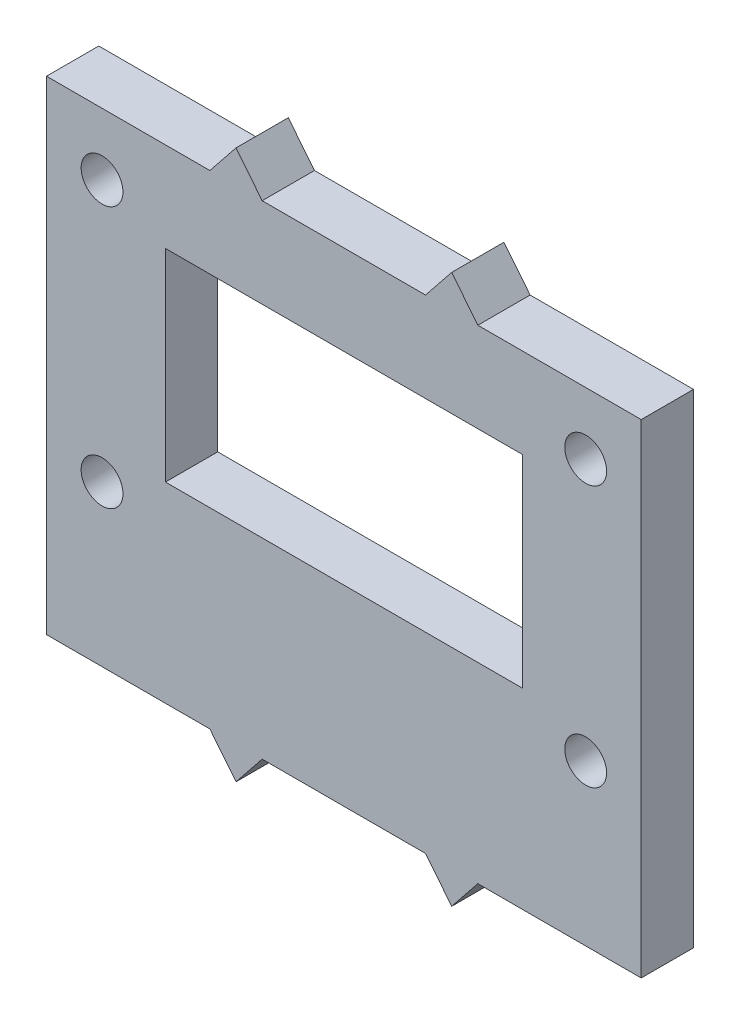
SolidWorks part; units mm, degrees
ref_plane "Front Plane" through (0, 0, 0) normal (0, 0, 1) x (1, 0, 0)
ref_plane "Top Plane" through (0, 0, 0) normal (0, 1, 0) x (1, 0, 0)
ref_plane "Right Plane" through (0, 0, 0) normal (1, 0, 0) x (0, 0, -1)
sketch "Sketch1" plane through (0, 0, 0) normal (0, 0, 1) x (1, 0, 0)
  line L0 (22.75, 37) -> (22.75, 14.7203) construction
  line L1 (0, 0) -> (45.5, 0)
  line L2 (0, 0) -> (0, 37)
  line L3 (0, 37) -> (45.5, 37)
  line L4 (45.5, 0) -> (45.5, 37)
  line L5 (12.5, 37) -> (14.5, 39.5)
  line L6 (14.5, 39.5) -> (16.5, 37)
  line L7 (31, 39.5) -> (29, 37)
  line L8 (33, 37) -> (31, 39.5)
  line L9 (0, 18.5) -> (57.9593, 18.5) construction
  line L10 (33, 0) -> (31, -2.5)
  line L11 (31, -2.5) -> (29, 0)
  line L12 (14.5, -2.5) -> (16.5, 0)
  line L13 (12.5, 0) -> (14.5, -2.5)
  point P9 (22.75, 37)
  point P16 (0, 18.5)
  point P17 (32, 38.25)
  point P18 (32, -1.25)
  dimension "D1" = 37
  dimension "D2" = 45.5
  dimension "D3" = 16.5
  dimension "D4" = 2.5
  dimension "D5" = 4
extrude "Basis" add sketch "Sketch1" along normal blind 4 contours L1 L4 L3 L2 | L6 L5 L3 | L3 L8 L7 | L1 L13 L12 | L11 L10 L1
sketch "Sketch2" [suppressed] plane through (0, 0, 4) normal (0, 0, 1) x (1, 0, 0)
  line L0 (16.5, 37) -> (29, 37) construction
  circle A0 centre (22.75, 23) radius 6.8
  point P5 (22.75, 37)
  dimension "D1" = 13.6
  dimension "D2" = 14
extrude "Camera gat " [suppressed] cut sketch "Sketch2" against normal up to surface (4 mm away)
sketch "Sketch5" [suppressed] plane through (0, 0, 4) normal (0, 0, 1) x (1, 0, 0)
  line L0 (8.6574, 7.1957) -> (36.8426, 7.1957) construction
  line L1 (16.5, 37) -> (29, 37) construction
  text T0 "camera" font "Bebas Kai" height 3.5
  point P2 (22.75, 7.1957)
  point P5 (22.75, 37)
extrude "Cut-Extrude4" [suppressed] cut sketch "Sketch5" against normal blind 0.2
sketch "Sketch3" [suppressed] plane through (0, 0, 4) normal (0, 0, 1) x (1, 0, 0)
  line L0 (22.75, 37) -> (22.75, 0) construction
  line L1 (16.5, 37) -> (29, 37) construction
  line L2 (16.5, 0) -> (29, 0) construction
  line L3 (0, 37) -> (12.5, 37) construction
  circle A0 centre (9.8, 25.6) radius 7.95
  circle A1 centre (35.7, 25.6) radius 7.95
  dimension "D3" = 15.9
  dimension "D1" = 11.4
  dimension "D2" = 25.9
extrude "HR04 gat " [suppressed] cut sketch "Sketch3" against normal up to surface (4 mm away)
sketch "Sketch4" [suppressed] plane through (0, 0, 4) normal (0, 0, 1) x (1, 0, 0)
  line L0 (7.7992, 12.9938) -> (37.7008, 12.9938) construction
  line L1 (16.5, 37) -> (29, 37) construction
  text T0 "AFSTAND SENSOR" font "Bebas Kai" height 3.5
  point P5 (22.75, 12.9938)
  point P8 (22.75, 37)
extrude "Afstand sensor" [suppressed] cut sketch "Sketch4" against normal blind 0.2
sketch "Sketch10" plane through (0, 0, 4) normal (0, 0, 1) x (1, 0, 0)
  line L1 (17.42, 29.57) -> (28.08, 29.57)
  line L2 (17.42, 29.57) -> (17.42, 34.43)
  line L3 (17.42, 34.43) -> (28.08, 34.43)
  line L4 (28.08, 29.57) -> (28.08, 34.43)
  line L5 (17.42, 29.57) -> (28.08, 34.43) construction
  line L6 (17.42, 34.43) -> (28.08, 29.57) construction
  line L9 (16.5, 37) -> (29, 37) construction
  point P4 (22.75, 32)
  point P5 (22.75, 37)
  point P6 (22.75, 34.43)
  dimension "D1" = 4.86
  dimension "D2" = 10.66
  dimension "D3" = 32
extrude "Press_fit" [suppressed] cut sketch "Sketch10" against normal blind 10
sketch "Sketch6" plane through (0, 0, 4) normal (0, 0, 1) x (1, 0, 0)
  line L4 (16.5, 37) -> (29, 37) construction
  point P0 (22.75, 30.14)
  point P3 (22.75, 37)
  line B0 (9.1, 30.14) -> (36.4, 30.14)
  line B1 (9.1, 30.14) -> (9.1, 14.6591)
  line B2 (9.1, 14.6591) -> (36.4, 14.6591)
  line B3 (36.4, 30.14) -> (36.4, 14.6591)
  circle B4 centre (11.1, 32.4381) radius 1.5
  circle B5 centre (34.4, 32.4381) radius 1.5
  circle B6 centre (34.4, 8.6381) radius 1.5
  circle B7 centre (11.1, 8.6381) radius 1.5
  dimension "D1" = 6.86
sketch_block_instance "Block1-1" [suppressed]
sketch_block "Block1" parameters "D1"=3, "D2"=3, "D3"=3, "D4"=3
extrude "Show only screen" cut sketch "Sketch6" against normal blind 10.04 contours B3 B0 B1 B2
sketch "Sketch7" [suppressed] plane through (0, 0, 4) normal (0, 0, 1) x (1, 0, 0)
  line L0 (-2.0092, 11.0348) -> (47.5092, 11.0348) construction
  line L1 (16.5, 37) -> (29, 37) construction
  text T0 "oled scherm " font "Bebas Kai" height 3.5
  point P4 (22.75, 37)
  point P5 (22.75, 11.0348)
extrude "Cut-Extrude6" [suppressed] cut sketch "Sketch7" against normal blind 0.2
sketch "Sketch11" plane through (0, 0, 0) normal (0, 0, -1) x (-1, 0, 0)
  line L0 (0, 0) -> (-45.5, 0) construction
  line L1 (-41.25, 32.2526) -> (-4.25, 32.2526) construction
  line L2 (-41.25, 32.2526) -> (-41.25, 12.2526) construction
  line L3 (-41.25, 12.2526) -> (-4.25, 12.2526) construction
  line L4 (-4.25, 32.2526) -> (-4.25, 12.2526) construction
  circle A0 centre (-41.25, 32.2526) radius 1.6
  circle A1 centre (-4.25, 32.2526) radius 1.6
  circle A2 centre (-4.25, 12.2526) radius 1.6
  circle A3 centre (-41.25, 12.2526) radius 1.6
  point P6 (-22.75, 12.2526)
  point P7 (-22.75, 0)
  dimension "D1" = 3.2
  dimension "D3" = 12.2526
  dimension "D4" = 20
  dimension "D5" = 37
extrude "Cut-Extrude10" cut sketch "Sketch11" against normal blind 4
